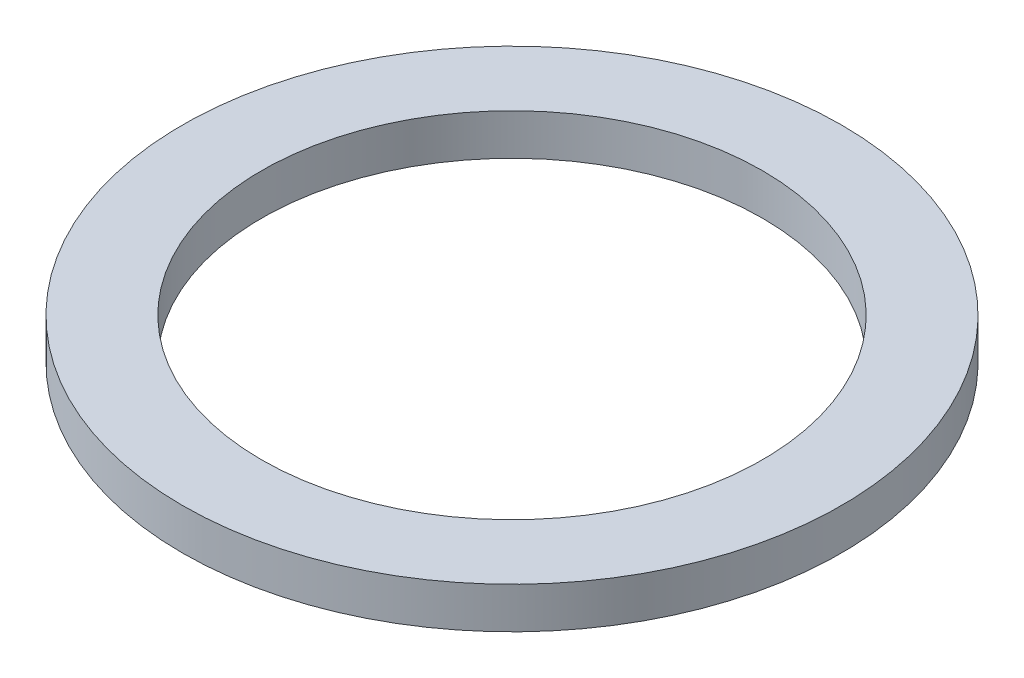
SolidWorks part; units mm, degrees
ref_plane "Front Plane" through (0, 0, 0) normal (0, 0, 1) x (1, 0, 0)
ref_plane "Top Plane" through (0, 0, 0) normal (0, 1, 0) x (1, 0, 0)
ref_plane "Right Plane" through (0, 0, 0) normal (1, 0, 0) x (0, 0, -1)
sketch "Sketch1" plane through (0, 0, 0) normal (0, 1, 0) x (1, 0, 0)
  circle A0 centre (0, 0) radius 12.7
  circle A1 centre (0, 0) radius 9.652
  dimension "D1" = 25.4
  dimension "D2" = 19.304
extrude "Boss-Extrude1" add sketch "Sketch1" along normal blind 1.5875
